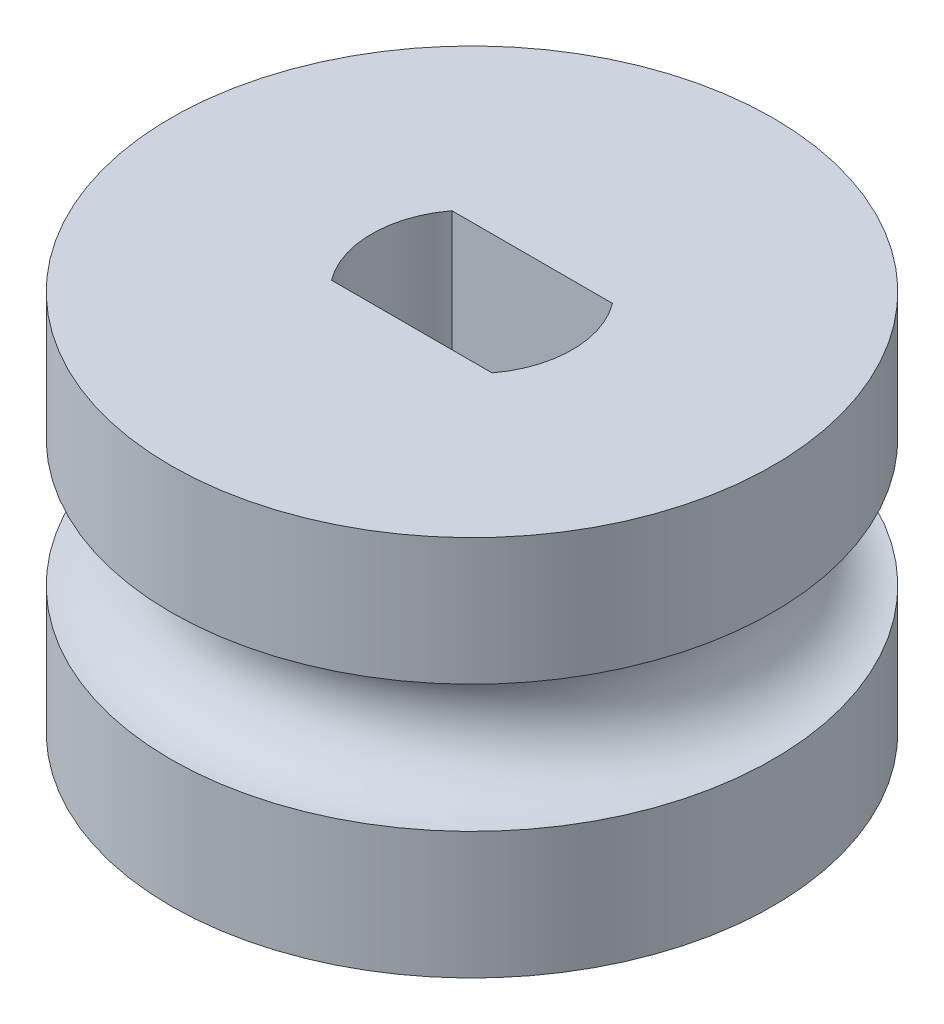
SolidWorks part; units mm, degrees
ref_plane "Front Plane" through (0, 0, 0) normal (0, 0, 1) x (1, 0, 0)
ref_plane "Top Plane" through (0, 0, 0) normal (0, 1, 0) x (1, 0, 0)
ref_plane "Right Plane" through (0, 0, 0) normal (1, 0, 0) x (0, 0, -1)
sketch "Sketch1" plane through (0, 0, 0) normal (0, 1, 0) x (1, 0, 0)
  line L0 (-2, 1.5) -> (2, 1.5)
  line L1 (-2, -1.5) -> (2, -1.5)
  circle A0 centre (0, 0) radius 7.5
  arc A1 (-2, 1.5) -> (-2, -1.5) centre (0, 0) ccw
  arc A2 (2, -1.5) -> (2, 1.5) centre (0, 0) ccw
  dimension "D1" = 5
  dimension "D2" = 15
  dimension "D3" = 3
extrude "Boss-Extrude1" add sketch "Sketch1" along normal blind 9.5
sketch "Sketch2" plane through (0, 0, 0) normal (0, 0, 1) x (1, 0, 0)
  line L0 (0, 9.5) -> (0, 0) construction
  line L1 (7.5, 9.5) -> (-7.5, 9.5) construction
  line L2 (7.5, 0) -> (7.5, 9.5) construction
  circle A0 centre (7.5, 4.75) radius 1.5875
  dimension "D1" = 3.175
revolve "Cut-Revolve1" cut sketch "Sketch2" angle 360 about L0
